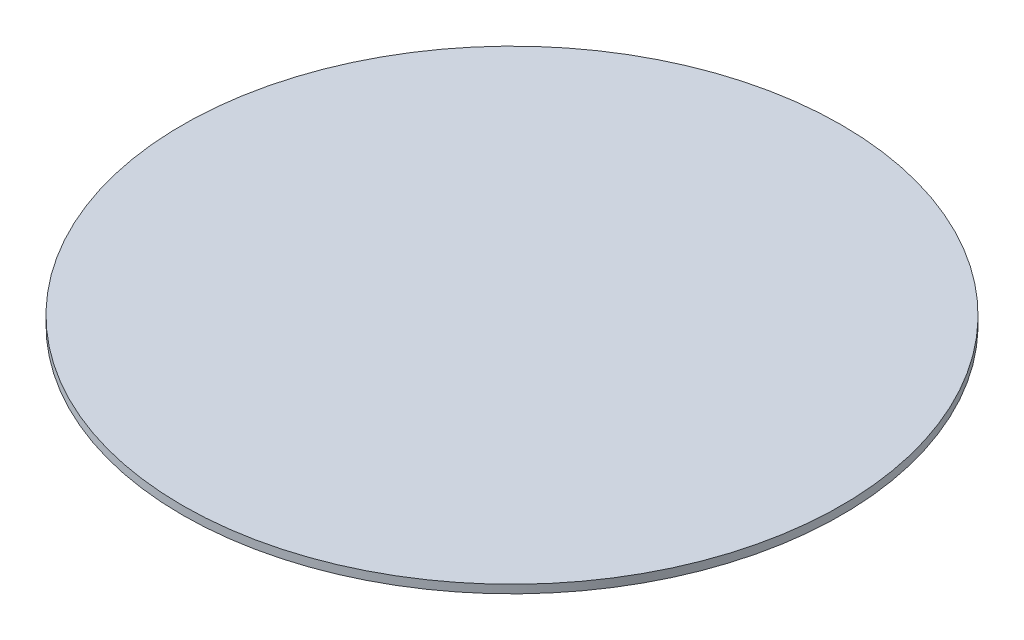
SolidWorks part; units mm, degrees
ref_plane "Front Plane" through (0, 0, 0) normal (0, 0, 1) x (1, 0, 0)
ref_plane "Top Plane" through (0, 0, 0) normal (0, 1, 0) x (1, 0, 0)
ref_plane "Right Plane" through (0, 0, 0) normal (1, 0, 0) x (0, 0, -1)
sketch "Sketch1" plane through (0, 0, 0) normal (0, 0, 1) x (1, 0, 0)
  line L0 (119, 3) -> (0, 3)
  line L1 (0, 3) -> (0, 0)
  line L2 (0, 0) -> (119, 0)
  line L3 (119, 0) -> (119, 3)
  line L4 (0, 3) -> (0, 0) construction
revolve "Revolve1" add sketch "Sketch1" angle 360 about L4
